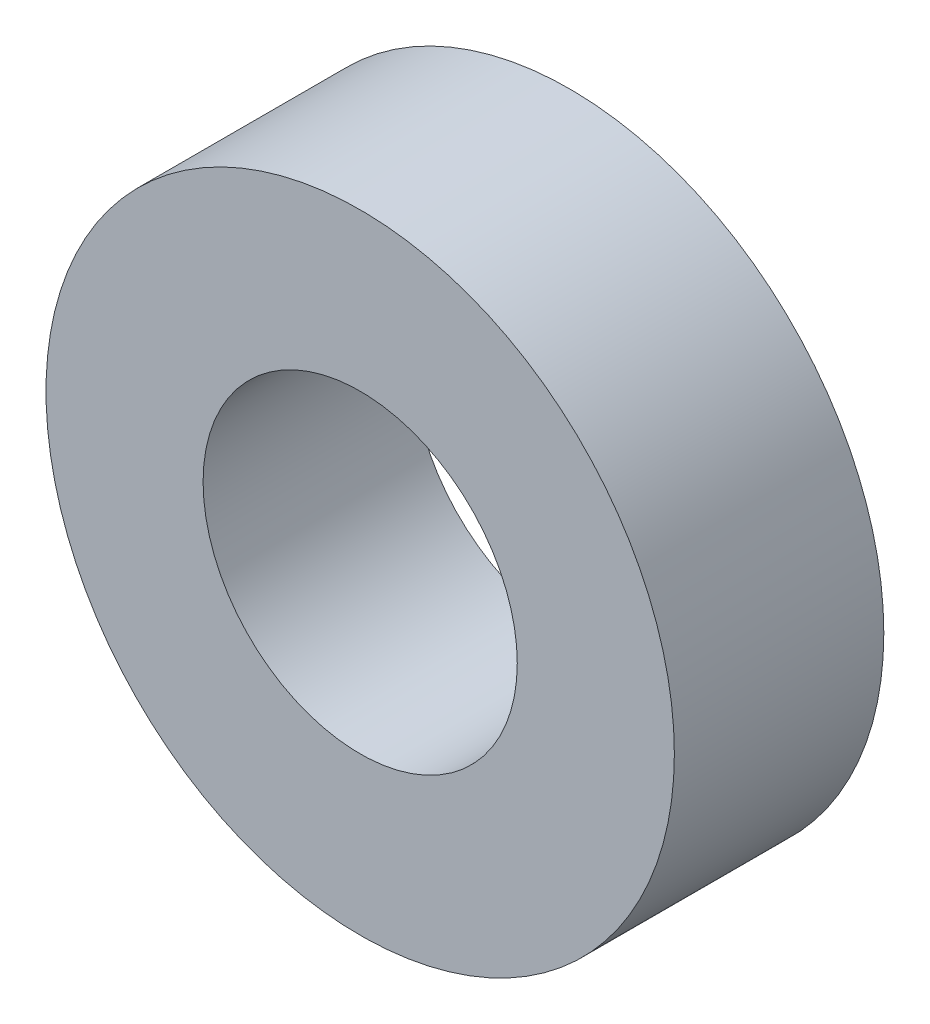
SolidWorks part; units mm, degrees
ref_plane "Front Plane" through (0, 0, 0) normal (0, 0, 1) x (1, 0, 0)
ref_plane "Top Plane" through (0, 0, 0) normal (0, 1, 0) x (1, 0, 0)
ref_plane "Right Plane" through (0, 0, 0) normal (1, 0, 0) x (0, 0, -1)
sketch "Sketch1" plane through (0, 0, 0) normal (0, 0, 1) x (1, 0, 0)
  circle A0 centre (256.1749, 227.3256) radius 2.3813
  circle A1 centre (256.1749, 227.3256) radius 4.7625
  dimension "D1" = 9.525
extrude "Boss-Extrude1" add sketch "Sketch1" along normal blind 3.175 contours A0 | A1
